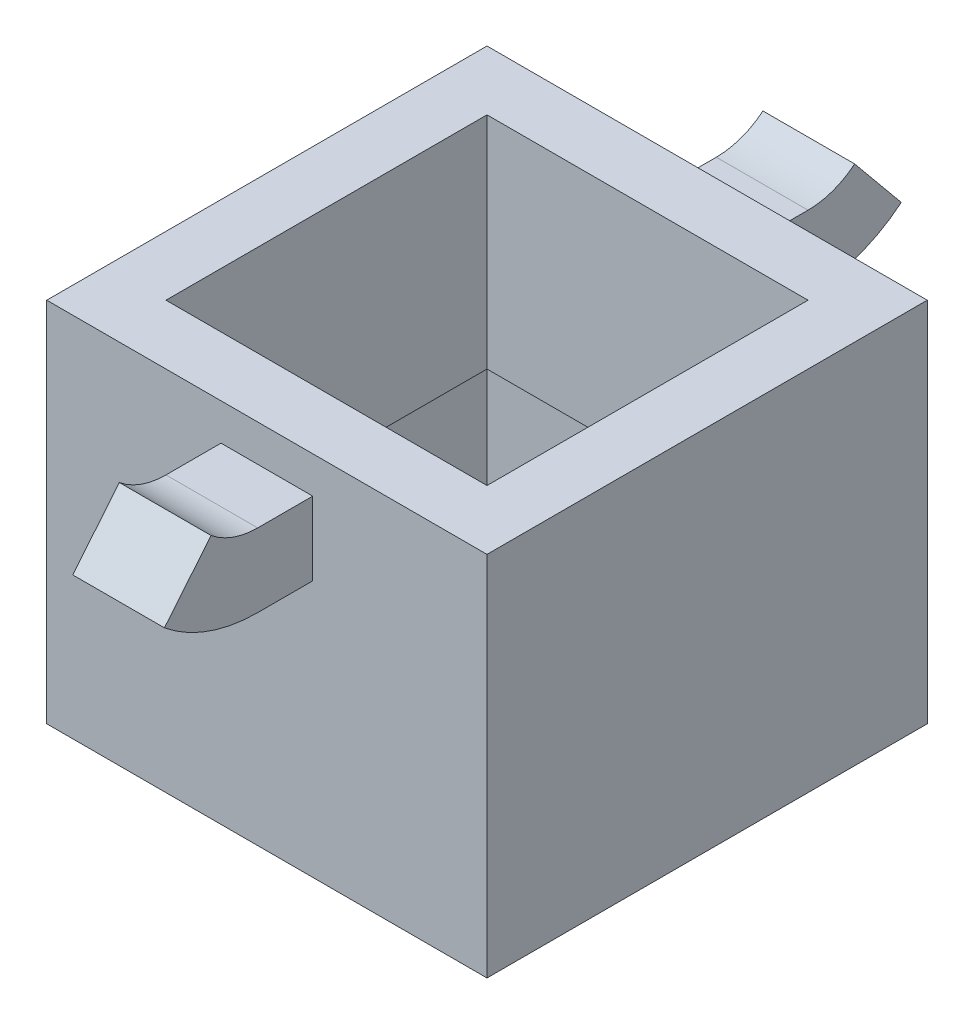
SolidWorks part; units mm, degrees
ref_plane "Front Plane" through (0, 0, 0) normal (0, 0, 1) x (1, 0, 0)
ref_plane "Top Plane" through (0, 0, 0) normal (0, 1, 0) x (1, 0, 0)
ref_plane "Right Plane" through (0, 0, 0) normal (1, 0, 0) x (0, 0, -1)
sketch "Sketch1" plane through (0, 0, 0) normal (0, 1, 0) x (1, 0, 0)
  line L1 (12, -12) -> (-12, -12)
  line L2 (12, -12) -> (12, 12)
  line L3 (12, 12) -> (-12, 12)
  line L4 (-12, -12) -> (-12, 12)
  line L5 (12, -12) -> (-12, 12) construction
  line L6 (12, 12) -> (-12, -12) construction
  point P0 (0, 0)
  dimension "D1" = 24
extrude "Boss-Extrude1" add sketch "Sketch1" along normal blind 20
sketch "Sketch3" plane through (0, 0, 0) normal (0, -1, 0) x (1, 0, 0)
  line L0 (-12, 12) -> (12, 12) construction
  line L1 (-10, -10) -> (10, -10)
  line L2 (-10, -10) -> (-10, 10)
  line L3 (-10, 10) -> (10, 10)
  line L4 (10, -10) -> (10, 10)
  line L5 (-10, -10) -> (10, 10) construction
  line L6 (-10, 10) -> (10, -10) construction
  point P0 (0, 0)
  dimension "D1" = 2
sketch "Sketch5" plane through (0, 0, -12) normal (0, 0, -1) x (-1, 0, 0)
  line L0 (-12, 0) -> (12, 20) construction
  line L1 (-12, 20) -> (12, 0) construction
  line L2 (0, 16) -> (0, 10) construction
  line L3 (2.5, 18) -> (-2.5, 18)
  line L4 (2.5, 18) -> (2.5, 14)
  line L5 (2.5, 14) -> (-2.5, 14)
  line L6 (-2.5, 18) -> (-2.5, 14)
  line L7 (2.5, 18) -> (-2.5, 14) construction
  line L8 (2.5, 14) -> (-2.5, 18) construction
  dimension "D1" = 5
  dimension "D2" = 4
  dimension "D3" = 6
sketch "Sketch6" plane through (0, 0, 0) normal (1, 0, 0) x (0, 0, -1)
  line L0 (12, 16) -> (15, 16)
  arc A0 (15, 16) -> (18.8134, 17.3677) centre (15, 22) ccw
  dimension "D2" = 6
  dimension "D1" = 3
sweep "Sweep1" add profiles "Sketch5" path "Sketch6"
mirror "Mirror1" about plane through (0, 0, 0) normal (0, 0, 1) of "Sweep1"
extrude "Cut-Extrude5" cut sketch "Sketch3" against normal blind 6
sketch "Sketch14" plane through (0, 6, 0) normal (0, -1, 0) x (1, 0, 0)
  line L1 (10, 10) -> (-10, 10)
  line L2 (10, 10) -> (10, -10)
  line L3 (10, -10) -> (-10, -10)
  line L4 (-10, 10) -> (-10, -10)
  line L5 (10, 10) -> (-10, -10) construction
  line L6 (10, -10) -> (-10, 10) construction
  point P0 (0, 0)
extrude "Cut-Extrude6" cut sketch "Sketch14" against normal blind 2
sketch "Sketch15" plane through (0, 8, 0) normal (0, -1, 0) x (1, 0, 0)
  line L1 (8.75, -8.75) -> (-8.75, -8.75)
  line L2 (8.75, -8.75) -> (8.75, 8.75)
  line L3 (8.75, 8.75) -> (-8.75, 8.75)
  line L4 (-8.75, -8.75) -> (-8.75, 8.75)
  line L5 (8.75, -8.75) -> (-8.75, 8.75) construction
  line L6 (8.75, 8.75) -> (-8.75, -8.75) construction
  line L7 (10, 10) -> (-10, 10) construction
  point P0 (0, 0)
  dimension "D1" = 1.25
extrude "Cut-Extrude7" cut sketch "Sketch15" against normal up to next
